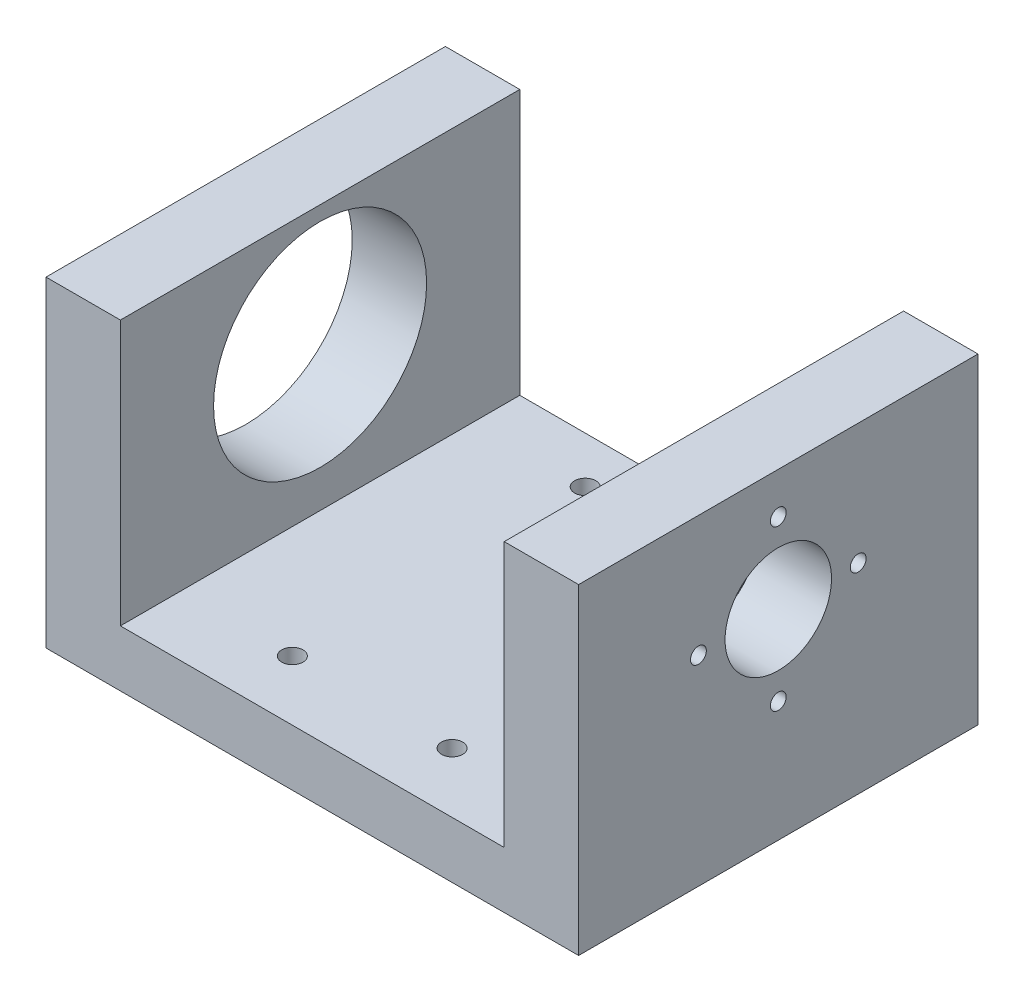
SolidWorks part; units mm, degrees
material "6061-T6 (SS)"
ref_plane "Front Plane" through (0, 0, 0) normal (0, 0, 1) x (1, 0, 0)
ref_plane "Top Plane" through (0, 0, 0) normal (0, 1, 0) x (1, 0, 0)
ref_plane "Right Plane" through (0, 0, 0) normal (1, 0, 0) x (0, 0, -1)
sketch "Sketch1" plane through (0, 0, 0) normal (0, 0, 1) x (1, 0, 0)
  line L1 (-16.6542, 14.8879) -> (23.3518, 14.8879)
  line L2 (-16.6542, 14.8879) -> (-16.6542, -9.2421)
  line L3 (-16.6542, -9.2421) -> (23.3518, -9.2421)
  line L4 (23.3518, 14.8879) -> (23.3518, -9.2421)
  dimension "D1" = 24.13
  dimension "D2" = 40.006
extrude "Boss-Extrude1" add sketch "Sketch1" along normal blind 30
sketch "Sketch2" plane through (0, 0, 30) normal (0, 0, 1) x (1, 0, 0)
  line L0 (-11.0662, 14.8879) -> (-11.0662, -5.0088)
  line L1 (23.3518, 14.8879) -> (-16.6542, 14.8879) construction
  line L2 (-11.0662, -5.0088) -> (17.7638, -5.0088)
  line L3 (17.7638, -5.0088) -> (17.7638, 14.8879)
  line L4 (-16.6542, 14.8879) -> (-16.6542, -9.2421) construction
  line L5 (-16.6542, -9.2421) -> (23.3518, -9.2421) construction
  line L6 (23.3518, -9.2421) -> (23.3518, 14.8879) construction
  dimension "D1" = 5.588
  dimension "D2" = 4.2333
  dimension "D3" = 5.588
sketch "Sketch6" plane through (0, 0, 30) normal (0, 0, 1) x (1, 0, 0)
  line L0 (17.7638, 14.8879) -> (17.7638, -5.0088)
  line L1 (17.7638, -5.0088) -> (-11.0662, -5.0088)
  line L2 (-11.0662, -5.0088) -> (-11.0662, 14.8879)
  line L3 (-11.0662, 14.8879) -> (17.7638, 14.8879)
extrude "Cut-Extrude1" cut sketch "Sketch6" against normal blind 30
sketch "Sketch9" plane through (0, -9.2421, 0) normal (0, -1, 0) x (-1, 0, 0)
  line L0 (-23.3518, 0) -> (16.6542, -30) construction
  line L1 (16.6542, 0) -> (-23.3518, -30) construction
  line L2 (-3.3488, -15) -> (-3.3488, -30) construction
  line L3 (11.0662, -30) -> (-17.7638, -30) construction
  line L4 (-3.3488, -15) -> (-3.3488, 0) construction
  line L5 (16.6542, 0) -> (-23.3518, 0) construction
  circle A0 centre (2.6512, -25.5) radius 0.8
  circle A1 centre (-9.3488, -25.5) radius 0.8
  circle A2 centre (-9.3488, -3.5) radius 0.8
  circle A3 centre (2.6512, -3.5) radius 0.8
  dimension "D3" = 1.6
  dimension "D4" = 1.6
  dimension "D7" = 1.6
  dimension "D8" = 1.6
  dimension "D1" = 4.5
  dimension "D2" = 4.5
  dimension "D5" = 22
  dimension "D6" = 22
  dimension "D9" = 6
  dimension "D10" = 6
  dimension "D11" = 6
  dimension "D12" = 6
extrude "Cut-Extrude3" cut sketch "Sketch9" against normal blind 30
sketch "Sketch21" plane through (23.3518, 0, 0) normal (1, 0, 0) x (0, 0, -1)
  line L0 (0, -9.2421) -> (0, 14.8879) construction
  circle A0 centre (-24.435, 0) radius 3.1242
  dimension "D1" = 24.435
  dimension "D2" = 6.2484
sketch "Sketch28" plane through (-16.6542, 0, 0) normal (-1, 0, 0) x (0, 0, 1)
  line L0 (30, -9.2421) -> (0, -9.2421) construction
  circle A0 centre (15, 5.7947) radius 3.1242
  dimension "D1" = 6.2484
  dimension "D2" = 15.0368
sketch "Sketch29" plane through (-16.6542, 0, 0) normal (-1, 0, 0) x (0, 0, 1)
  circle A0 centre (15, 5.7947) radius 8.001
  dimension "D1" = 16.002
sketch "Sketch30" plane through (-16.6542, 0, 0) normal (-1, 0, 0) x (0, 0, 1)
extrude "Cut-Extrude4" cut sketch "Sketch29" against normal blind 5.588
sketch "Sketch41" plane through (23.3518, 0, 0) normal (1, 0, 0) x (0, 0, -1)
  line L0 (-15, 3.5342) -> (-15, 8.9189) construction
  line L1 (-18.1242, 5.7947) -> (-11.8758, 5.7947) construction
  circle A0 centre (-15, 5.7947) radius 3.1242 construction
  circle A1 centre (-15, 5.7947) radius 4
  point P0 (-15, 12.2947)
  point P1 (-21, 5.7947)
  point P9 (-15, -0.7053)
  point P10 (-9, 5.7947)
  dimension "D3" = 8
  dimension "D1" = 6.5
  dimension "D2" = 6
extrude "Cut-Extrude5" cut sketch "Sketch41" against normal up to surface (5.588 mm away) up to face at (17.7638, 4.9395, 15)
hole_wizard "#0-80 Tapped Hole1" positions "Sketch45" profile "Sketch44" tap size "#0-80" standard "ANSI Inch" end condition up to next
sketch "Sketch45" plane through (23.3518, 0, 0) normal (1, 0, 0) x (0, 0, -1)
  line L0 (-15, 5.7947) -> (-9, 5.7947) construction
  line L3 (-15, 5.7947) -> (-15, 11.7947) construction
  circle A0 centre (-15, 5.7947) radius 4 construction
  point P0 (-15, 11.7947)
  point P6 (-9, 5.7947)
  point P50 (-15, -0.2053)
  point P51 (-21, 5.7947)
  dimension "D1" = 12
sketch "Sketch44" plane through (23.3518, 11.7947, 15) normal (0, 1, 0) x (0, 0, -1)
  line L0 (0, 0) -> (0, 5.588)
  line L1 (0, 5.588) -> (0.5956, 5.588)
  line L2 (0.5956, 5.588) -> (0.5956, 0)
  line L5 (0.5956, 0) -> (0, 0)
  line L11 (0, -6.35) -> (0, 107.95) construction
  dimension "Thread Major Dia." = 1.1913
  dimension "Thru Tap Drill Depth" = 5.588
